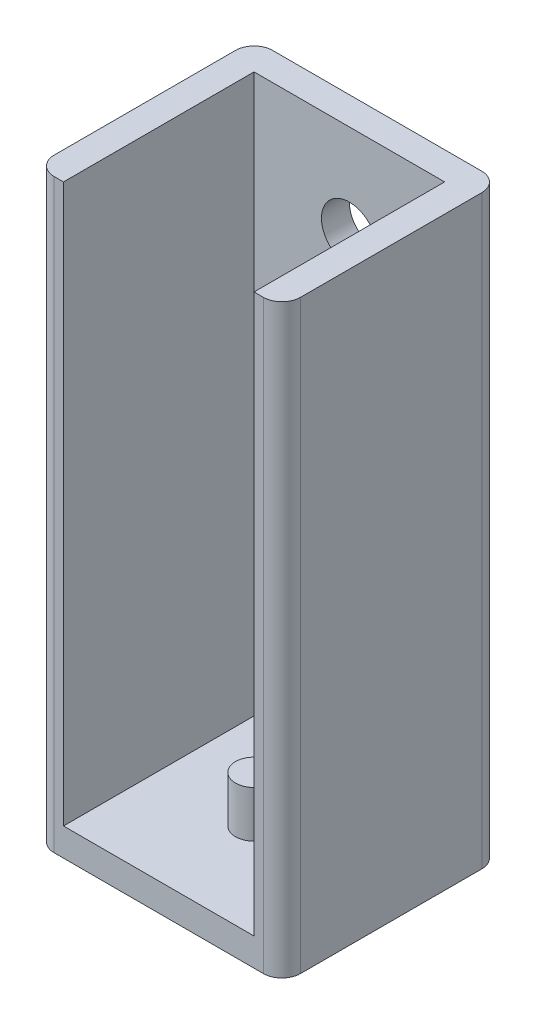
SolidWorks part; units mm, degrees
ref_plane "Front Plane" through (0, 0, 0) normal (0, 0, 1) x (1, 0, 0)
ref_plane "Top Plane" through (0, 0, 0) normal (0, 1, 0) x (1, 0, 0)
ref_plane "Right Plane" through (0, 0, 0) normal (1, 0, 0) x (0, 0, -1)
sketch "Sketch1" plane through (0, 0, 0) normal (0, 1, 0) x (1, 0, 0)
  line L0 (-13.25, -8.25) -> (-13.25, 11.25)
  line L1 (-10.25, -10.25) -> (10.25, -10.25)
  line L2 (-10.25, -10.25) -> (-10.25, 10.25)
  line L3 (-10.25, 10.25) -> (10.25, 10.25)
  line L4 (10.25, -10.25) -> (10.25, 10.25)
  line L5 (-10.25, -10.25) -> (10.25, 10.25) construction
  line L6 (-10.25, 10.25) -> (10.25, -10.25) construction
  line L7 (-11.25, 13.25) -> (11.25, 13.25)
  line L8 (13.25, -8.25) -> (13.25, 11.25)
  line L10 (-13.25, -13.25) -> (-13.25, 13.25) construction
  line L11 (-11.25, -10.25) -> (11.25, -10.25)
  line L12 (13.25, -13.25) -> (13.25, 13.25) construction
  line L13 (-13.25, -13.25) -> (13.25, -13.25) construction
  line L14 (-13.25, 13.25) -> (13.25, 13.25) construction
  arc A0 (-13.25, 11.25) -> (-11.25, 13.25) centre (-11.25, 11.25) cw
  arc A1 (11.25, 13.25) -> (13.25, 11.25) centre (11.25, 11.25) cw
  arc A2 (11.25, -10.25) -> (13.25, -8.25) centre (11.25, -8.25) ccw
  arc A3 (-13.25, -8.25) -> (-11.25, -10.25) centre (-11.25, -8.25) ccw
  point P0 (0, 0)
  dimension "D4" = 2
  dimension "D1" = 20.5
  dimension "D2" = 20.5
  dimension "D3" = 3
extrude "Boss-Extrude1" add sketch "Sketch1" along normal blind 60 contours L0 A3 L11 L2 L3 L4 A2 L8 A1 L7 A0
sketch "Sketch2" plane through (0, 0, 0) normal (0, -1, 0) x (1, 0, 0)
  line L1 (-10.25, -10.25) -> (10.25, -10.25)
  line L2 (-10.25, -10.25) -> (-10.25, 10.25)
  line L3 (-10.25, 10.25) -> (10.25, 10.25)
  line L4 (10.25, -10.25) -> (10.25, 10.25)
  line L5 (-10.25, -10.25) -> (10.25, 10.25) construction
  line L6 (-10.25, 10.25) -> (10.25, -10.25) construction
  line L14 (-13.25, 8.25) -> (-13.25, -11.25)
  line L15 (-11.25, -13.25) -> (11.25, -13.25)
  line L16 (13.25, -11.25) -> (13.25, 8.25)
  line L17 (11.25, 10.25) -> (10.25, 10.25)
  line L18 (10.25, 10.25) -> (10.25, -10.25)
  line L19 (10.25, -10.25) -> (-10.25, -10.25)
  line L20 (-10.25, -10.25) -> (-10.25, 10.25)
  line L21 (-10.25, 10.25) -> (-11.25, 10.25)
  line L22 (-13.25, 8.25) -> (-13.25, -11.25)
  line L23 (-11.25, -13.25) -> (11.25, -13.25)
  line L24 (13.25, -11.25) -> (13.25, 8.25)
  line L25 (11.25, 10.25) -> (10.25, 10.25)
  line L26 (10.25, 10.25) -> (10.25, -10.25)
  line L27 (10.25, -10.25) -> (-10.25, -10.25)
  line L28 (-10.25, -10.25) -> (-10.25, 10.25)
  line L29 (-10.25, 10.25) -> (-11.25, 10.25)
  arc A4 (-13.25, -11.25) -> (-11.25, -13.25) centre (-11.25, -11.25) ccw
  arc A5 (11.25, -13.25) -> (13.25, -11.25) centre (11.25, -11.25) ccw
  arc A6 (13.25, 8.25) -> (11.25, 10.25) centre (11.25, 8.25) ccw
  arc A7 (-11.25, 10.25) -> (-13.25, 8.25) centre (-11.25, 8.25) ccw
  arc A8 (-13.25, -11.25) -> (-11.25, -13.25) centre (-11.25, -11.25) ccw
  arc A9 (11.25, -13.25) -> (13.25, -11.25) centre (11.25, -11.25) ccw
  arc A10 (13.25, 8.25) -> (11.25, 10.25) centre (11.25, 8.25) ccw
  arc A11 (-11.25, 10.25) -> (-13.25, 8.25) centre (-11.25, 8.25) ccw
  point P0 (0, 0)
  line M13 (-13.25, 8.25) -> (-13.25, -11.25)
  arc M14 (-13.25, -11.25) -> (-11.25, -13.25) centre (-11.25, -11.25) ccw
  line M15 (-11.25, -13.25) -> (11.25, -13.25)
  arc M16 (11.25, -13.25) -> (13.25, -11.25) centre (11.25, -11.25) ccw
  line M17 (13.25, -11.25) -> (13.25, 8.25)
  arc M18 (13.25, 8.25) -> (11.25, 10.25) centre (11.25, 8.25) ccw
  line M19 (11.25, 10.25) -> (10.25, 10.25)
  line M20 (10.25, 10.25) -> (10.25, -10.25)
  line M21 (10.25, -10.25) -> (-10.25, -10.25)
  line M22 (-10.25, -10.25) -> (-10.25, 10.25)
  line M23 (-10.25, 10.25) -> (-11.25, 10.25)
  arc M24 (-11.25, 10.25) -> (-13.25, 8.25) centre (-11.25, 8.25) ccw
  dimension "D1" = 0
extrude "Boss-Extrude2" add sketch "Sketch2" along normal blind 3 contours M24 M13 M14 M15 M16 M17 M18 M19 M20 M21 M22 M23 | L3 M22 M21 M20
sketch "Sketch3" plane through (0, 0, 0) normal (0, 1, 0) x (1, 0, 0)
  circle A0 centre (0, 0) radius 2
extrude "Boss-Extrude3" add sketch "Sketch3" along normal blind 5
sketch "Sketch4" plane through (0, 0, -13.25) normal (0, 0, -1) x (-1, 0, 0)
  line L0 (0, 60) -> (0, -3) construction
  line L1 (11.25, 60) -> (-11.25, 60) construction
  line L2 (11.25, -3) -> (-11.25, -3) construction
  circle A0 centre (0, 50) radius 3
  circle A1 centre (0, 17) radius 3
  dimension "D1" = 10
  dimension "D2" = 20
extrude "Cut-Extrude1" cut sketch "Sketch4" against normal up to surface (23.5 mm away) up to face at (0, 29.25, 10.25)
